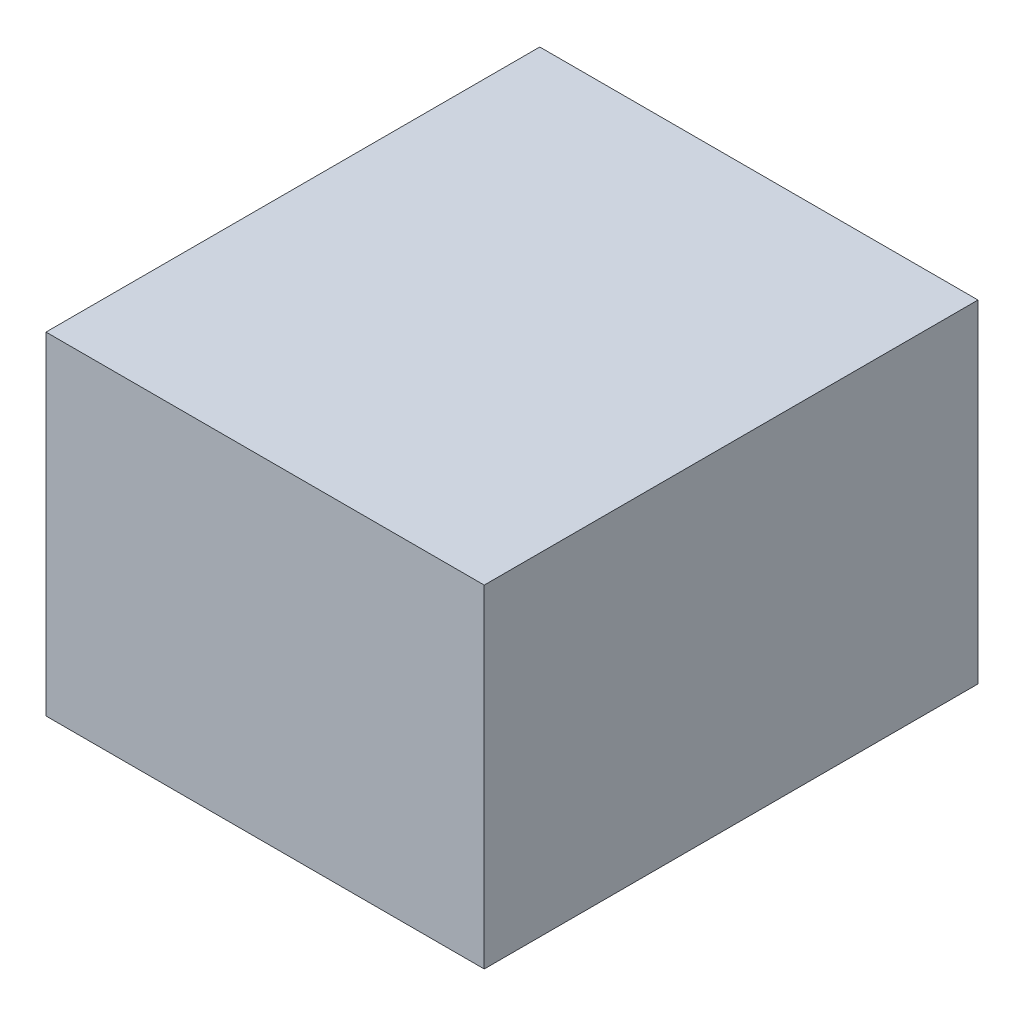
SolidWorks part; units mm, degrees
ref_plane "Front Plane" through (0, 0, 0) normal (0, 0, 1) x (1, 0, 0)
ref_plane "Top Plane" through (0, 0, 0) normal (0, 1, 0) x (1, 0, 0)
ref_plane "Right Plane" through (0, 0, 0) normal (1, 0, 0) x (0, 0, -1)
sketch "Sketch1" plane through (0, 0, 0) normal (0, 1, 0) x (1, 0, 0)
  line L0 (-111.76, 0) -> (-111.76, 9.42)
  line L1 (0, 0) -> (-111.76, 0)
  line L2 (0, 0) -> (0, 75.69)
  line L3 (0, 75.69) -> (-111.76, 75.69)
  line L4 (-111.76, 0) -> (-111.76, 9.42)
  line L5 (-111.76, 9.42) -> (-100.58, 9.42)
  line L7 (-111.76, 16.28) -> (-100.58, 16.28)
  line L8 (-111.76, 16.28) -> (-111.76, 75.69)
  line L9 (0, 0) -> (0, 37.845)
  line L10 (0, 37.845) -> (-111.76, 37.845)
  line L11 (-55.88, 75.69) -> (-55.88, 0)
  line L12 (-111.76, 66.27) -> (-100.58, 66.27)
  line L13 (-111.76, 59.41) -> (-100.58, 59.41)
  line L14 (0, 9.42) -> (-11.18, 9.42)
  line L15 (0, 16.28) -> (-11.18, 16.28)
  line L16 (0, 59.41) -> (-11.18, 59.41)
  line L17 (0, 66.27) -> (-11.18, 66.27)
  arc A0 (-100.58, 9.42) -> (-100.58, 16.28) centre (-100.58, 12.85) ccw
  arc A1 (-100.58, 66.27) -> (-100.58, 59.41) centre (-100.58, 62.84) cw
  arc A2 (-11.18, 9.42) -> (-11.18, 16.28) centre (-11.18, 12.85) cw
  arc A3 (-11.18, 66.27) -> (-11.18, 59.41) centre (-11.18, 62.84) ccw
  dimension "D1" = 111.76
  dimension "D2" = 75.69
sketch "Sketch2" plane through (0, 0, 0) normal (0, 1, 0) x (1, 0, 0)
  line L0 (-55.88, 0) -> (-55.88, 75.69)
  line L1 (-111.76, 0) -> (-121.76, 0)
  line L2 (-111.76, 0) -> (-111.76, -10)
  line L3 (-111.76, -10) -> (-121.76, -10)
  line L4 (-121.76, 0) -> (-121.76, -10)
  line L5 (0, 75.69) -> (10, 75.69)
  line L6 (0, 75.69) -> (0, 85.69)
  line L7 (0, 85.69) -> (10, 85.69)
  line L8 (10, 75.69) -> (10, 85.69)
  line L9 (-111.76, 37.845) -> (0, 37.845)
  circle A0 centre (-100.58, 12.85) radius 3.43
  circle A1 centre (-100.58, 12.85) radius 8
  circle A2 centre (-100.58, 62.84) radius 8
  circle A3 centre (-11.18, 12.85) radius 8
  circle A4 centre (-11.18, 62.84) radius 8
  dimension "D1" = 10
  dimension "D2" = 10
  dimension "D3" = 10
  dimension "D4" = 10
sketch "Sketch3" plane through (0, 0, 0) normal (0, 1, 0) x (1, 0, 0)
  line L0 (-100.58, 54.84) -> (-92.58, 54.84)
  line L1 (-121.76, -10) -> (-108.58, -10)
  line L2 (-121.76, -10) -> (-121.76, 12.85)
  line L5 (-108.58, -10) -> (-11.18, -10)
  line L9 (10, 85.69) -> (-3.18, 85.69)
  line L10 (10, 85.69) -> (10, 62.84)
  line L14 (10, 62.84) -> (10, -10)
  line L15 (10, -10) -> (-3.18, -10)
  line L19 (-11.18, -10) -> (-3.18, -10)
  line L22 (-121.76, 12.85) -> (-121.76, 62.84)
  line L26 (-121.76, 62.84) -> (-121.76, 85.69)
  line L27 (-121.76, 85.69) -> (-108.58, 85.69)
  line L29 (-108.58, 85.69) -> (-11.18, 85.69)
  line L35 (-11.18, 85.69) -> (-3.18, 85.69)
  line L37 (-92.58, 62.84) -> (-92.58, 54.84)
  line L38 (-19.18, 12.85) -> (-19.18, 20.85)
  line L39 (-11.18, 20.85) -> (-19.18, 20.85)
  line L41 (-92.58, 54.84) -> (-19.18, 54.84)
  line L42 (-92.58, 54.84) -> (-92.58, 20.85)
  line L43 (-92.58, 20.85) -> (-19.18, 20.85)
  line L44 (-19.18, 54.84) -> (-19.18, 20.85)
  circle A1 centre (-11.18, 12.85) radius 8 construction
  circle A3 centre (-100.58, 62.84) radius 8 construction
  circle A4 centre (-100.58, 62.84) radius 8
  circle A5 centre (-11.18, 62.84) radius 8
  circle A6 centre (-11.18, 12.85) radius 8
  circle A7 centre (-100.58, 12.85) radius 8
sketch "Sketch4" plane through (0, 0, 0) normal (0, 1, 0) x (1, 0, 0)
  line L0 (-108.58, 62.84) -> (-108.58, 70.84)
  line L1 (-108.58, 12.85) -> (-108.58, 4.85)
  line L2 (-108.58, 70.84) -> (-121.76, 70.84)
  line L3 (-108.58, 70.84) -> (-108.58, 85.69)
  line L4 (-108.58, 85.69) -> (-121.76, 85.69)
  line L5 (-121.76, 70.84) -> (-121.76, 85.69)
  line L6 (-55.88, 0) -> (-55.88, 75.69)
  line L7 (-108.58, 4.85) -> (-121.76, 4.85)
  line L8 (-108.58, 4.85) -> (-108.58, -10)
  line L9 (-108.58, -10) -> (-121.76, -10)
  line L10 (-121.76, 4.85) -> (-121.76, -10)
  line L11 (0, 0) -> (-111.76, 0) construction
  line L12 (10, 4.85) -> (10, -10)
  line L13 (-3.18, -10) -> (10, -10)
  line L14 (-3.18, 4.85) -> (-3.18, -10)
  line L15 (-3.18, 4.85) -> (10, 4.85)
  line L16 (-3.18, 70.84) -> (10, 70.84)
  line L17 (10, 70.84) -> (10, 85.69)
  line L18 (-3.18, 85.69) -> (10, 85.69)
  line L19 (-3.18, 70.84) -> (-3.18, 85.69)
  circle A0 centre (-100.58, 62.84) radius 8 construction
  circle A1 centre (-100.58, 12.85) radius 8 construction
extrude "Boss-Extrude2" add sketch "Sketch4" along normal blind 10 contours L5 L2 L3 L4
sketch "Sketch5" plane through (0, 0, 0) normal (0, -1, 0) x (1, 0, 0)
  line L0 (-108.58, -78.265) -> (-121.76, -78.265)
  line L1 (-108.58, -70.84) -> (-108.58, -85.69) construction
  line L2 (-121.76, -62.84) -> (-121.76, -85.69) construction
  circle A0 centre (-115.17, -78.265) radius 5
extrude "Cut-Extrude1" cut sketch "Sketch5" against normal blind 5 contours L0 A0 | L0 A0
sketch "Sketch6" plane through (0, 5, 0) normal (0, -1, 0) x (1, 0, 0)
  line L0 (-115.17, -73.265) -> (-115.17, -83.265)
  circle A0 centre (-115.17, -78.265) radius 5 construction
  circle A1 centre (-115.17, -78.265) radius 5 construction
  circle A2 centre (-115.17, -78.265) radius 3
